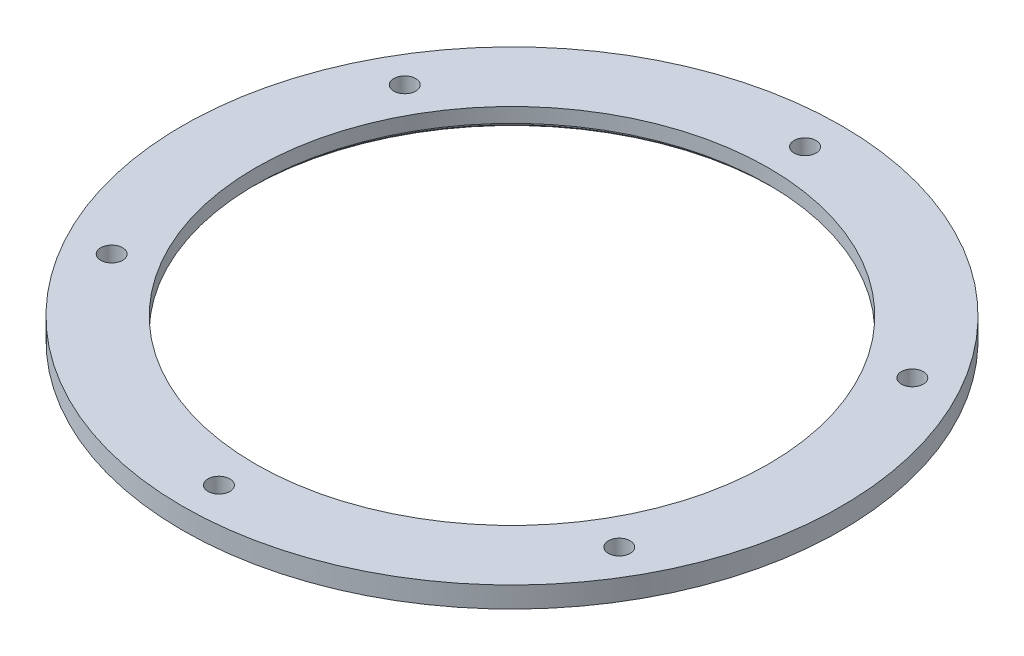
SolidWorks part; units mm, degrees
ref_plane "Front Plane" through (0, 0, 0) normal (0, 0, 1) x (1, 0, 0)
ref_plane "Top Plane" through (0, 0, 0) normal (0, 1, 0) x (1, 0, 0)
ref_plane "Right Plane" through (0, 0, 0) normal (1, 0, 0) x (0, 0, -1)
sketch "Sketch1" plane through (0, 0, 0) normal (0, 1, 0) x (1, 0, 0)
  circle A0 centre (0, 0) radius 158
  circle A1 centre (0, 0) radius 123
  circle A2 centre (0, 0) radius 140.5 construction
  circle A3 centre (0, 140.5) radius 5.25
  circle A4 centre (121.6766, 70.25) radius 5.25
  circle A5 centre (121.6766, -70.25) radius 5.25
  circle A6 centre (0, -140.5) radius 5.25
  circle A7 centre (-121.6766, -70.25) radius 5.25
  circle A8 centre (-121.6766, 70.25) radius 5.25
  point P19 (0, 0)
  dimension "D1" = 246
  dimension "D2" = 316
  dimension "D3" = 281
  dimension "D4" = 10.5
  dimension "D5" = 6
extrude "Boss-Extrude1" add sketch "Sketch1" along normal blind 10
sketch "Sketch2" plane through (0, 0, 0) normal (0, -1, 0) x (1, 0, 0)
  circle A0 centre (0, 0) radius 125
  dimension "D1" = 250
extrude "Cut-Extrude1" cut sketch "Sketch2" against normal blind 3
chamfer "Chamfer1" distance 1 angle 45 1 edges at (0, 0, -125)
sketch "Sketch3" plane through (0, 0, 0) normal (0, -1, 0) x (1, 0, 0)
  line L0 (-121.6766, -70.25) -> (121.6766, 70.25) construction
